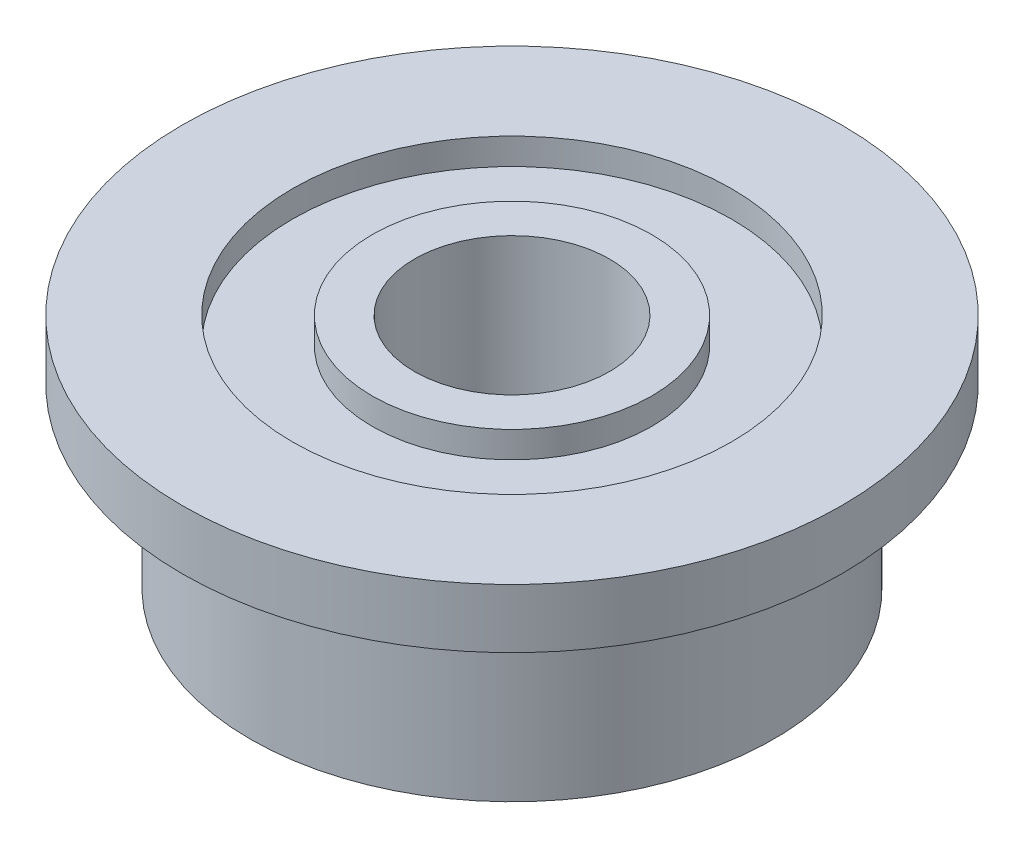
SolidWorks part; units mm, degrees
ref_plane "Front Plane" through (0, 0, 0) normal (0, 0, 1) x (1, 0, 0)
ref_plane "Top Plane" through (0, 0, 0) normal (0, 1, 0) x (1, 0, 0)
ref_plane "Right Plane" through (0, 0, 0) normal (1, 0, 0) x (0, 0, -1)
sketch "Sketch1" plane through (0, 0, 0) normal (0, 0, 1) x (1, 0, 0)
  line L0 (0, 0) -> (0, -3.4264) construction
  line L1 (3.125, 0) -> (2.08, 0)
  line L2 (2.48, -2.24) -> (2.48, -0.56)
  line L3 (2.48, -0.56) -> (3.125, -0.56)
  line L4 (3.125, -0.56) -> (3.125, 0)
  line L5 (2.08, 0) -> (2.08, -0.25)
  line L6 (2.08, -0.25) -> (1.325, -0.25)
  line L7 (1.325, -0.25) -> (1.325, 0)
  line L8 (1.325, 0) -> (0.925, 0)
  line L9 (0.925, 0) -> (0.925, -2.24)
  line L10 (0.925, -2.24) -> (1.325, -2.24)
  line L11 (1.325, -2.24) -> (1.325, -1.99)
  line L12 (1.325, -1.99) -> (2.08, -1.99)
  line L13 (2.08, -1.99) -> (2.08, -2.24)
  line L14 (2.08, -2.24) -> (2.48, -2.24)
  dimension "D1" = 0.4
  dimension "D2" = 4.96
  dimension "D3" = 0.4
  dimension "D4" = 1.85
  dimension "D5" = 0.25
  dimension "D6" = 6.25
  dimension "D7" = 0.56
  dimension "D8" = 2.24
revolve "Revolve1" add sketch "Sketch1" angle 360 about L0
sketch "Sketch2" plane through (0, 0, 0) normal (0, 0, 1) x (1, 0, 0)
  line L0 (0, 0) -> (0, -2.24)
  line L1 (-2.48, -2.24) -> (2.48, -2.24) construction
  line L2 (0, -1.12) -> (3.496, -1.12)
ref_plane "Plane1" through (0, -1.12, 0) normal (0, 1, 0) x (1, 0, 0)
ref_plane "Plane2" through (0, -1.25, 0) normal (0, 1, 0) x (1, 0, 0)
sketch "Sketch3" plane through (0, -1.25, 0) normal (0, 1, 0) x (1, 0, 0)
  line L0 (-2.48, -2.48) -> (9.52, -2.48) construction
  line L1 (-2.48, -2.48) -> (-2.48, 13.5123) construction
  line L2 (-2.6883, -2.48) -> (-0.8748, 19.9802) construction
  line L3 (-2.48, -2.48) -> (-2.48, -28.0738) construction
  circle A0 centre (0, 0) radius 2.48 construction
  circle A2 centre (0, 0) radius 2.48 construction
  dimension "D2" = 12
ref_plane "Plane3" through (-2.48, 0, 0) normal (1, 0, 0) x (0, 0, -1)
ref_plane "Plane4" through (0, -1.25, 0) normal (0, 1, 0) x (1, 0, 0)
ref_point "Point1"
ref_plane "Plane5" through (0, -0.75, 0) normal (0, 1, 0) x (1, 0, 0)
sketch "Sketch4" plane through (0, -0.75, 0) normal (0, 1, 0) x (1, 0, 0)
  line L0 (0, -2.48) -> (-14.6, -2.48)
  line L1 (2.4469, 0.4037) -> (1.212, 7.8887)
  circle A0 centre (0, 0) radius 2.48 construction
  dimension "D1" = 14.6
